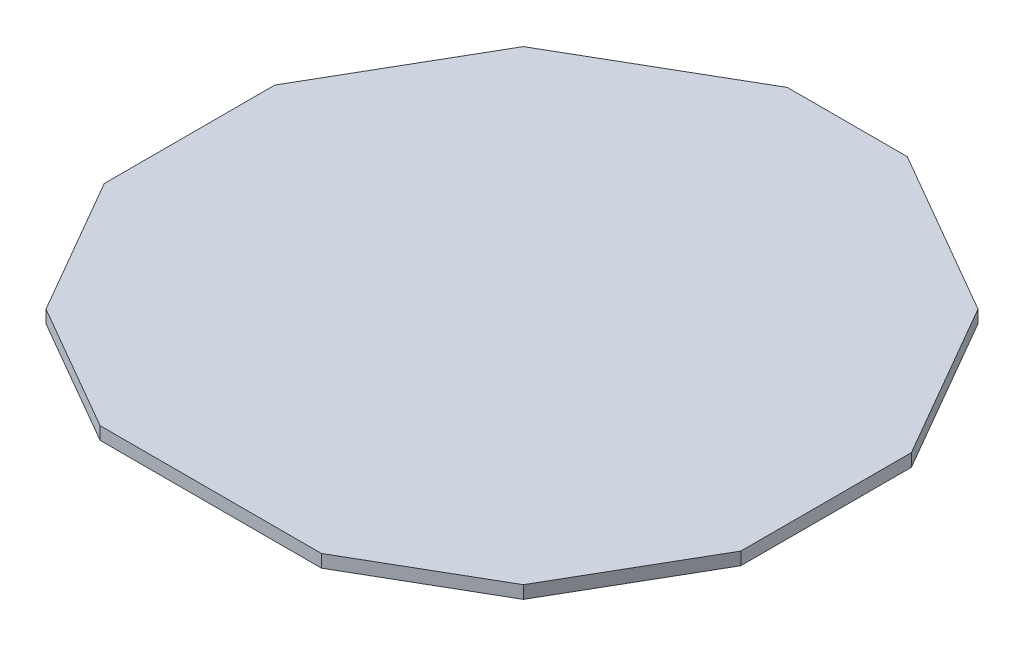
SolidWorks part; units mm, degrees
ref_plane "Ebene vorne" through (0, 0, 0) normal (0, 0, 1) x (1, 0, 0)
ref_plane "Ebene oben" through (0, 0, 0) normal (0, 1, 0) x (1, 0, 0)
ref_plane "Ebene rechts" through (0, 0, 0) normal (1, 0, 0) x (0, 0, -1)
sketch "Skizze1" plane through (0, 0, 0) normal (0, 1, 0) x (1, 0, 0)
  line L0 (0, 0) -> (0, 50) construction
  line L1 (-40, 30) -> (40, 30)
  line L2 (0, 0) -> (25, 43.3013) construction
  line L3 (0, 0) -> (43.3013, 25) construction
  line L4 (0, 0) -> (50, 0) construction
  line L5 (0, 0) -> (43.3013, -25) construction
  line L6 (0, 0) -> (25, -43.3013) construction
  line L7 (0, 0) -> (0, -50) construction
  line L8 (0, 0) -> (-25, -43.3013) construction
  line L9 (0, 0) -> (-43.3013, -25) construction
  line L10 (0, 0) -> (-50, 0) construction
  line L11 (0, 0) -> (-43.3013, 25) construction
  line L12 (0, 0) -> (-25, 43.3013) construction
  line L13 (-49.8446, 3.9387) -> (21.5113, 45.1361)
  line L14 (-1.9464, 49.9621) -> (-44.2416, -23.2954)
  line L15 (-25, 43.3013) -> (-25, -43.3013)
  line L16 (-42.3181, 26.6304) -> (1.9036, -49.9638)
  line L17 (-49.8579, 3.767) -> (28.1912, -41.2947)
  line L18 (-45.8258, -20) -> (45.8258, -20)
  line L19 (-28.1912, -41.2947) -> (49.8579, 3.767)
  line L20 (-1.9036, -49.9638) -> (42.3181, 26.6304)
  line L21 (25, -43.3013) -> (25, 43.3013)
  line L22 (44.2416, -23.2954) -> (1.9464, 49.9621)
  line L23 (-21.5113, 45.1361) -> (49.8446, 3.9387)
  circle A0 centre (0, 0) radius 5 construction
  circle A1 centre (0, 0) radius 50
  point P20 (0, 0)
  point P41 (1.4546, 49.8843)
extrude "Aufsatz-Linear austragen1" add sketch "Skizze1" along normal blind 1 contours L21 L22 L18 L14 L15 L16 L17 L19 L20
equation "\"min\"= 20"
equation "\"max\"= 30"
equation "\"KantenAnzahl\"= 12"
equation "\"teiler\" =  ( \"max\" - \"min\" )  /  ( \"KantenAnzahl\" / 2 ) "
equation "\"D2@Skizze1\"= ( \"max\" + \"min\" ) * 2"
equation "\"D1@Skizze1\"= \"max\" - \"min\""
equation "\"D4@Skizze1\"= \"KantenAnzahl\""
equation "\"D3@Skizze1\"= \"max\""
equation "\"D11@Skizze1\"= \"D3@Skizze1\" - \"teiler\""
equation "\"D5@Skizze1\"= \"D3@Skizze1\" - \"teiler\""
equation "\"D12@Skizze1\"= \"D11@Skizze1\" - \"teiler\""
equation "\"D6@Skizze1\"= \"D5@Skizze1\" - \"teiler\""
equation "\"D13@Skizze1\"= \"D12@Skizze1\" - \"teiler\""
equation "\"D7@Skizze1\"= \"D6@Skizze1\" - \"teiler\""
equation "\"D14@Skizze1\"= \"D13@Skizze1\" - \"teiler\""
equation "\"D8@Skizze1\" = \"D7@Skizze1\" - \"teiler\""
equation "\"D15@Skizze1\"= \"D14@Skizze1\" - \"teiler\""
equation "\"D9@Skizze1\"= \"D8@Skizze1\" - \"teiler\""
equation "\"D10@Skizze1\"= \"D9@Skizze1\" - \"teiler\""
